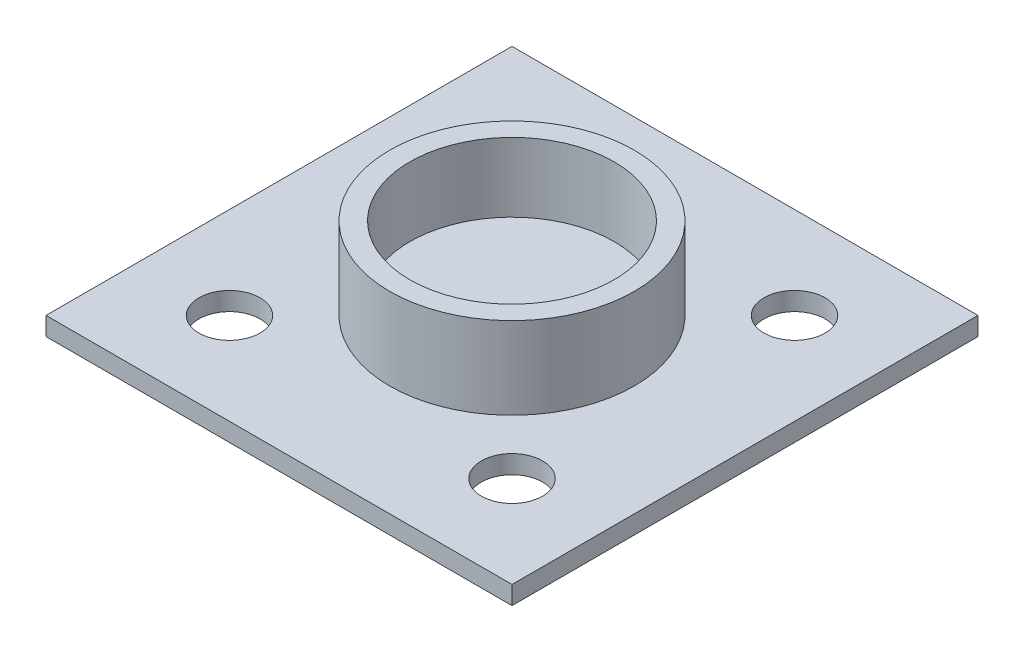
SolidWorks part; units mm, degrees
ref_plane "Plan de face" through (0, 0, 0) normal (0, 0, 1) x (1, 0, 0)
ref_plane "Plan de dessus" through (0, 0, 0) normal (0, 1, 0) x (1, 0, 0)
ref_plane "Plan de droite" through (0, 0, 0) normal (1, 0, 0) x (0, 0, -1)
sketch "Esquisse1" plane through (0, 0, 0) normal (0, 1, 0) x (1, 0, 0)
  circle A0 centre (0, 0) radius 10
  dimension "D1" = 20
extrude "Boss.-Extru.1" add sketch "Esquisse1" against normal blind 8.2
sketch "Esquisse2" plane through (0, 0, 0) normal (0, 1, 0) x (1, 0, 0)
  circle A0 centre (0, 0) radius 8.354
  dimension "D1" = 16.708
extrude "Enlèv. mat.-Extru.1" cut sketch "Esquisse2" against normal blind 5.65
sketch "Esquisse3" plane through (0, -8.2, 0) normal (0, -1, 0) x (-1, 0, 0)
  line L1 (19.05, -19.05) -> (-19.05, -19.05)
  line L2 (19.05, -19.05) -> (19.05, 19.05)
  line L3 (19.05, 19.05) -> (-19.05, 19.05)
  line L4 (-19.05, -19.05) -> (-19.05, 19.05)
  line L5 (19.05, -19.05) -> (-19.05, 19.05) construction
  line L6 (19.05, 19.05) -> (-19.05, -19.05) construction
  point P0 (0, 0)
  dimension "D1" = 38.1
  dimension "D2" = 38.1
extrude "Boss.-Extru.3" add sketch "Esquisse3" against normal blind 1.5
sketch "Esquisse4" plane through (0, -6.7, 0) normal (0, 1, 0) x (1, 0, 0)
  line L0 (-19.05, 19.05) -> (19.05, 19.05) construction
  line L1 (-19.05, -19.05) -> (-19.05, 19.05) construction
  circle A0 centre (-11.55, 11.55) radius 2.5
  circle A1 centre (11.55, 11.55) radius 2.5
  circle A2 centre (11.55, -11.55) radius 2.5
  circle A3 centre (-11.55, -11.55) radius 2.5
  point P15 (0, 0)
  dimension "D1" = 5
  dimension "D2" = 7.5
  dimension "D3" = 7.5
  dimension "D4" = 4
extrude "Enlèv. mat.-Extru.2" cut sketch "Esquisse4" against normal blind 2
equation "\"D1@Esquisse1\"=20mm"
equation "\"D1@Esquisse2\"=16.2mm + 20mil"
